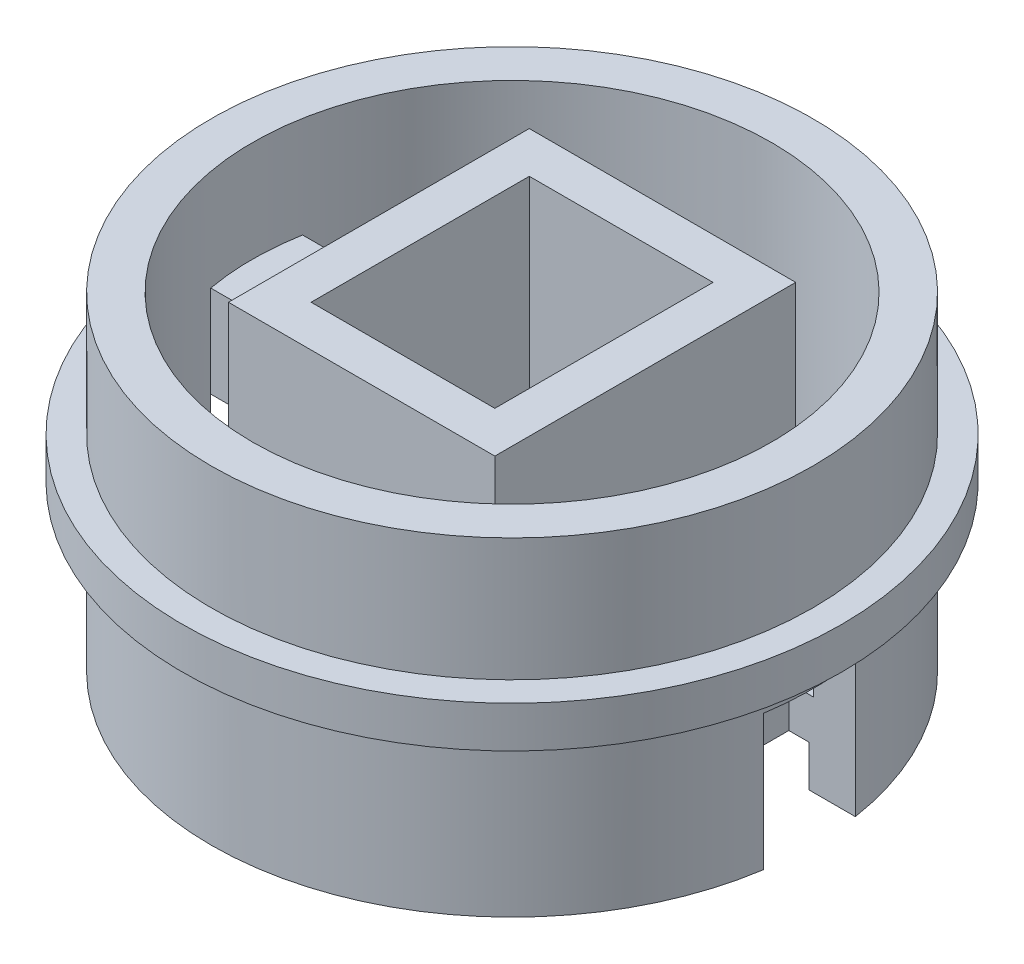
SolidWorks part; units mm, degrees
material "ABS"
ref_plane "Front Plane" through (0, 0, 0) normal (0, 0, 1) x (1, 0, 0)
ref_plane "Top Plane" through (0, 0, 0) normal (0, 1, 0) x (1, 0, 0)
ref_plane "Right Plane" through (0, 0, 0) normal (1, 0, 0) x (0, 0, -1)
sketch "Sketch1" plane through (0, 0, 0) normal (0, 1, 0) x (1, 0, 0)
  line L1 (-5.08, -6.0325) -> (5.08, -6.0325)
  line L2 (-5.08, -6.0325) -> (-5.08, 6.0325)
  line L3 (-5.08, 6.0325) -> (5.08, 6.0325)
  line L4 (5.08, -6.0325) -> (5.08, 6.0325)
  line L5 (-5.08, -6.0325) -> (5.08, 6.0325) construction
  line L6 (-5.08, 6.0325) -> (5.08, -6.0325) construction
  circle A0 centre (0, 0) radius 22.225 construction
  circle A1 centre (0, 0) radius 16.637
  point P0 (0, 0)
  dimension "D2" = 44.45
  dimension "D1" = 12.065
  dimension "D4" = 10.16
  dimension "D3" = 5.588
extrude "Boss-Extrude1" add sketch "Sketch1" along normal blind 15.875
shell "Shell1" thickness 2.286
sketch "Sketch2" plane through (0, 0, 0) normal (0, -1, 0) x (1, 0, 0)
  line L1 (-5.08, 6.0325) -> (-1.905, 6.0325)
  line L2 (-5.08, 6.0325) -> (5.08, 6.0325) construction
  line L3 (-1.905, 6.0325) -> (-5.08, 2.8575)
  line L4 (-5.08, -6.0325) -> (-5.08, 6.0325) construction
  line L5 (-5.08, 2.8575) -> (-5.08, 6.0325)
  line L6 (5.08, -2.8575) -> (1.905, -6.0325)
  line L7 (5.08, 6.0325) -> (5.08, -6.0325) construction
  line L8 (5.08, -6.0325) -> (-5.08, -6.0325) construction
  line L9 (1.905, -6.0325) -> (5.08, -6.0325)
  line L10 (5.08, -6.0325) -> (5.08, -2.8575)
  dimension "D1" = 3.175
extrude "Boss-Extrude2" add sketch "Sketch2" against normal blind 1.5875
sketch "Sketch3" plane through (0, 15.875, 0) normal (0, 1, 0) x (1, 0, 0)
  line L0 (-12.7635, 0) -> (0, 0) construction
  line L1 (-14.351, 2.54) -> (-12.7635, 2.54)
  line L2 (-14.351, 2.54) -> (-14.351, -2.54)
  line L3 (-14.351, -2.54) -> (-12.7635, -2.54)
  line L4 (-12.7635, 2.54) -> (-12.7635, -2.54)
  circle A0 centre (0, 0) radius 14.351 construction
  dimension "D1" = 5.08
  dimension "D2" = 1.5875
extrude "Boss-Extrude3" add sketch "Sketch3" against normal up to surface (13.589 mm away) up to face at (0, 2.286, 14.351)
sketch "Sketch7" plane through (0, 0, 0) normal (0, -1, 0) x (1, 0, 0)
  circle A0 centre (0, 0) radius 16.637 construction
  circle A1 centre (0, 0) radius 16.637
  circle A2 centre (0, 0) radius 14.097
  dimension "D1" = 2.54
extrude "Boss-Extrude4" add sketch "Sketch7" along normal blind 2.286
sketch "Sketch4" plane through (0, -2.286, 0) normal (0, -1, 0) x (1, 0, 0)
  line L0 (-14.351, -2.54) -> (-12.7635, -2.54) construction
  line L1 (-12.7635, -2.54) -> (-12.7635, 2.54) construction
  line L2 (-14.351, 2.54) -> (-12.7635, 2.54) construction
  line L3 (-16.442, -2.54) -> (-12.7635, -2.54)
  line L4 (-12.7635, -2.54) -> (-12.7635, 2.54)
  line L5 (-16.442, 2.54) -> (-12.7635, 2.54)
  circle A0 centre (0, 0) radius 16.637 construction
  arc A1 (-16.442, 2.54) -> (-16.442, -2.54) centre (0, 0) ccw
extrude "Cut-Extrude1" cut sketch "Sketch4" against normal offset from surface (7.493 mm away) 10.668 up to face at (-6.3251, 15.875, 0)
sketch "Sketch5" plane through (0, 15.875, 0) normal (0, 1, 0) x (1, 0, 0)
  line L0 (-16.442, -2.54) -> (-12.7635, -2.54) construction
  line L1 (-16.442, 2.54) -> (-12.7635, 2.54) construction
  line L2 (-12.7635, 2.54) -> (-12.7635, -2.54) construction
  line L3 (-14.1244, -2.54) -> (-12.7635, -2.54)
  line L4 (-14.1244, 2.54) -> (-12.7635, 2.54)
  line L5 (-12.7635, 2.54) -> (-12.7635, -2.54)
  arc A0 (-14.1244, -2.54) -> (-14.1244, 2.54) centre (0, 0) ccw construction
  arc A1 (-14.1244, 2.54) -> (-14.1244, -2.54) centre (0, 0) ccw
extrude "Cut-Extrude2" cut sketch "Sketch5" against normal blind 5.588
pattern_circular "CirPattern2" count 2 over 360 about axis through (0, 0, 0) along (0, 1, 0) of "Boss-Extrude3", "Cut-Extrude1", "Cut-Extrude2"
sketch "Sketch6" plane through (0, 0, 0) normal (0, 0, 1) x (1, 0, 0)
  line L0 (-16.637, 15.875) -> (-16.637, 5.207) construction
  line L1 (-16.637, 9.0805) -> (-18.2245, 9.0805)
  line L2 (-16.637, 9.0805) -> (-16.637, 6.7945)
  line L3 (-16.637, 6.7945) -> (-18.2245, 6.7945)
  line L4 (-18.2245, 9.0805) -> (-18.2245, 6.7945)
  line L5 (0, 0) -> (0, 15.875) construction
  line L6 (16.637, 15.875) -> (-16.637, 15.875) construction
  line L7 (0, 7.9375) -> (-16.637, 7.9375) construction
  dimension "D1" = 2.286
  dimension "D2" = 1.5875
revolve "Revolve1" add sketch "Sketch6" angle 360 about L5
